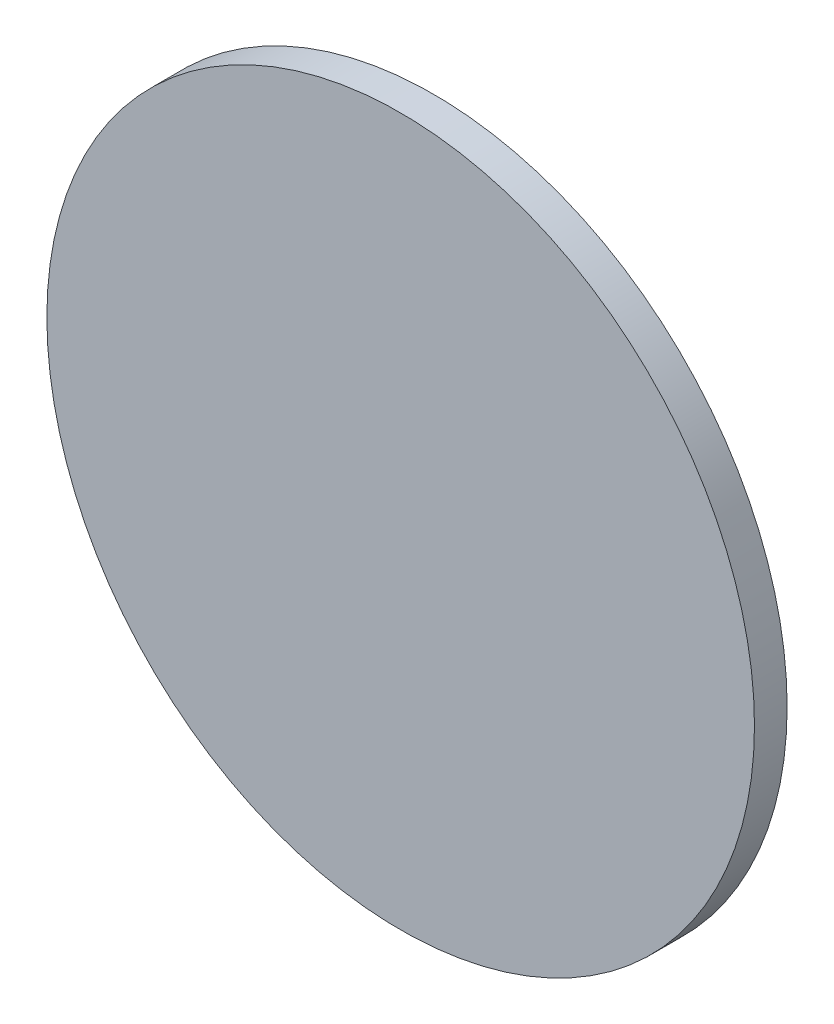
SolidWorks part; units mm, degrees
ref_plane "Front Plane" through (0, 0, 0) normal (0, 0, 1) x (1, 0, 0)
ref_plane "Top Plane" through (0, 0, 0) normal (0, 1, 0) x (1, 0, 0)
ref_plane "Right Plane" through (0, 0, 0) normal (1, 0, 0) x (0, 0, -1)
sketch "Sketch1" plane through (0, 0, 0) normal (0, 0, 1) x (1, 0, 0)
  circle A0 centre (0, 0) radius 65
  dimension "D1" = 130
extrude "Boss-Extrude1" add sketch "Sketch1" along normal blind 6
